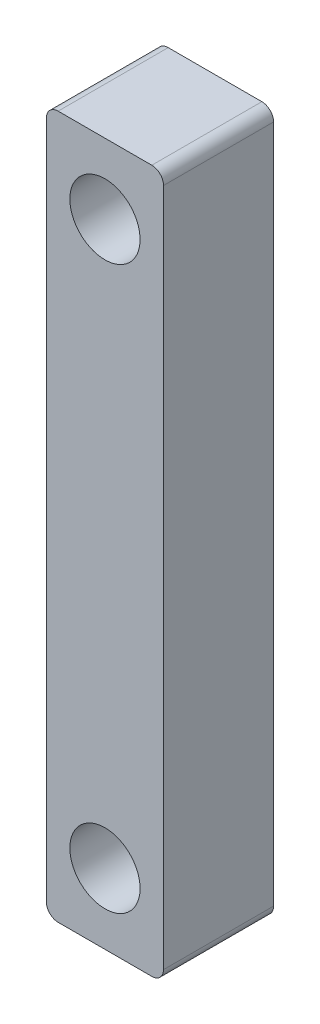
SolidWorks part; units mm, degrees
material "ABS"
ref_plane "Front Plane" through (0, 0, 0) normal (0, 0, 1) x (1, 0, 0)
ref_plane "Top Plane" through (0, 0, 0) normal (0, 1, 0) x (1, 0, 0)
ref_plane "Right Plane" through (0, 0, 0) normal (1, 0, 0) x (0, 0, -1)
sketch "Sketch1" plane through (0, 0, 0) normal (0, 0, 1) x (1, 0, 0)
  line L0 (0.5, 0) -> (4.5, 0)
  line L1 (0, -0.5) -> (0, -29.5)
  line L2 (5, -0.5) -> (5, -29.5)
  line L3 (0.5, -30) -> (4.5, -30)
  arc A0 (5, -29.5) -> (4.5, -30) centre (4.5, -29.5) cw
  arc A1 (0, -29.5) -> (0.5, -30) centre (0.5, -29.5) ccw
  arc A2 (4.5, 0) -> (5, -0.5) centre (4.5, -0.5) cw
  arc A3 (0, -0.5) -> (0.5, 0) centre (0.5, -0.5) cw
  point P7 (5, -30)
  point P12 (5, 0)
  point P15 (0, 0)
  dimension "D3" = 0.5
  dimension "D1" = 5
  dimension "D2" = 30
extrude "Boss-Extrude1" add sketch "Sketch1" along normal blind 4.7
sketch "Sketch2" plane through (0, 0, 4.7) normal (0, 0, 1) x (1, 0, 0)
  line L0 (0, -15) -> (9.631, -15) construction
  line L1 (0, -0.5) -> (0, -29.5) construction
  line L2 (4.5, 0) -> (0.5, 0) construction
  circle A0 centre (2.5, -27) radius 1.5
  circle A1 centre (2.5, -3) radius 1.5
  point P10 (2.5, 0)
  dimension "D1" = 3
  dimension "D2" = 3
extrude "Cut-Extrude1" cut sketch "Sketch2" against normal through all
